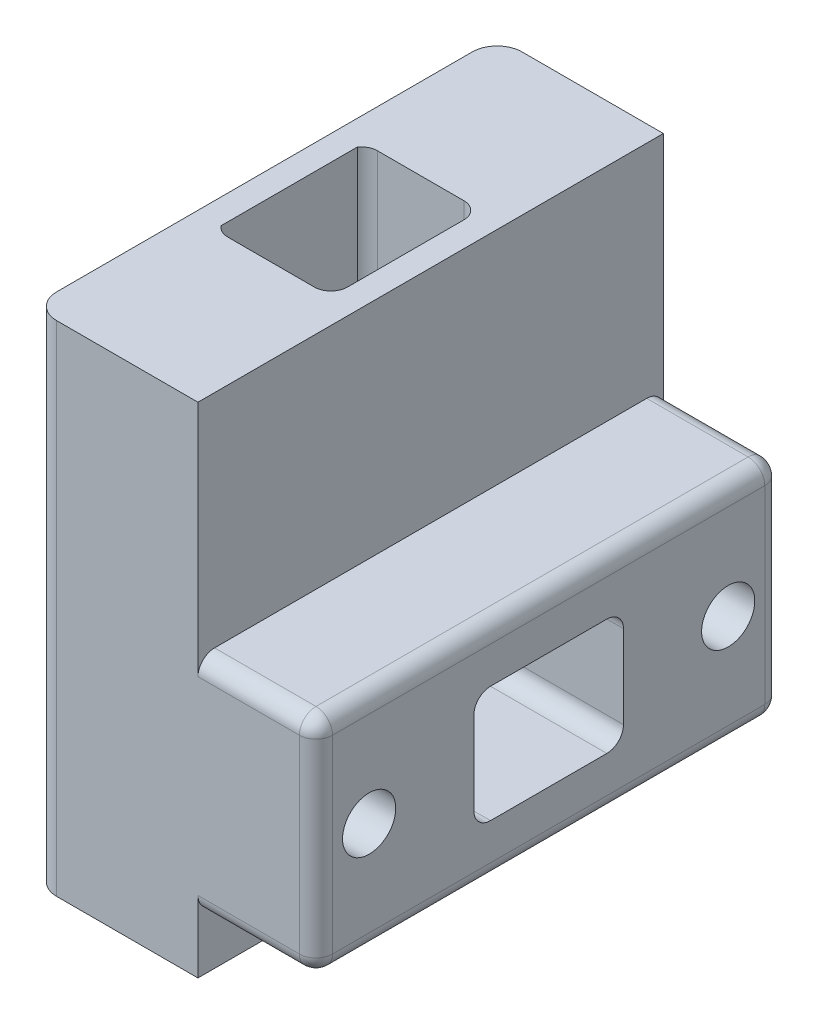
SolidWorks part; units mm, degrees
material "ABS"
ref_plane "前视基准面" through (0, 0, 0) normal (0, 0, 1) x (1, 0, 0)
ref_plane "上视基准面" through (0, 0, 0) normal (0, 1, 0) x (1, 0, 0)
ref_plane "右视基准面" through (0, 0, 0) normal (1, 0, 0) x (0, 0, -1)
sketch "草图1" plane through (0, 0, 0) normal (0, 0, 1) x (1, 0, 0)
  line L0 (0, 30) -> (0, 0)
  line L2 (17.1, 3.3) -> (17.1, 16.7)
  line L3 (17.1, 16.7) -> (10, 16.7)
  line L4 (10, 16.7) -> (10, 30)
  line L5 (10, 30) -> (0, 30)
  line L6 (17.1, 3.3) -> (10, 3.3)
  line L7 (10, 3.3) -> (10, 0)
  line L8 (10, 0) -> (0, 0)
  dimension "D1" = 13.4
  dimension "D2" = 7.1
  dimension "D3" = 13.3
  dimension "D4" = 10
  dimension "D5" = 3.3
extrude "凸台-拉伸1" add sketch "草图1" along normal blind 28 contours L0 L8 L7 L6 L2 L3 L4 L5
sketch "草图2" plane through (17.1, 0, 0) normal (1, 0, 0) x (0, 0, -1)
  line L0 (-28, 10) -> (14.4567, 10) construction
  line L1 (-28, 3.3) -> (-28, 16.7) construction
  line L2 (-14, 16.7) -> (-14, -6.8669) construction
  line L3 (-28, 16.7) -> (0, 16.7) construction
  circle A0 centre (-24.8, 10) radius 1.6
  circle A1 centre (-3.2, 10) radius 1.6
  dimension "D1" = 3.2
  dimension "D2" = 21.6
extrude "切除-拉伸1" cut sketch "草图2" against normal through all and the other way through all
sketch "草图4" plane through (17.1, 0, 0) normal (1, 0, 0) x (0, 0, -1)
  line L0 (0, 10) -> (-37.4348, 10) construction
  line L1 (0, 3.3) -> (0, 16.7) construction
  line L2 (-14, 16.7) -> (-14, -3.8155) construction
  line L3 (-28, 16.7) -> (0, 16.7) construction
  line L5 (-18.5, 13.5) -> (-9.5, 13.5)
  line L6 (-18.5, 13.5) -> (-18.5, 6.5)
  line L7 (-18.5, 6.5) -> (-9.5, 6.5)
  line L8 (-9.5, 13.5) -> (-9.5, 6.5)
  dimension "D1" = 7
  dimension "D2" = 9
extrude "切除-拉伸2" cut sketch "草图4" against normal blind 15.8
sketch "草图5" plane through (0, 30, 0) normal (0, 1, 0) x (1, 0, 0)
  line L0 (5, -28) -> (5, 6.0502) construction
  line L1 (10, -28) -> (0, -28) construction
  line L2 (0, -14) -> (16.5551, -14) construction
  line L3 (0, -28) -> (0, 0) construction
  line L5 (1.5, -18.5) -> (8.5, -18.5)
  line L6 (1.5, -18.5) -> (1.5, -9.5)
  line L7 (1.5, -9.5) -> (8.5, -9.5)
  line L8 (8.5, -18.5) -> (8.5, -9.5)
  dimension "D1" = 9
  dimension "D2" = 7
extrude "切除-拉伸3" cut sketch "草图5" against normal blind 23 contours L8 L7 L6 L5
fillet "圆角1" radius 1.5 2 edges at (0, 15, 28) (0, 15, 0)
fillet "圆角2" radius 1 10 edges at (8.5, 13.5, 14) (8.5, 21.75, 18.5) (8.5, 21.75, 9.5) (12.8, 13.5, 18.5) (12.8, 13.5, 9.5) (9.2, 6.5, 9.5) (9.2, 6.5, 18.5) (1.3, 6.5, 14) (1.3, 10, 18.5) (1.3, 10, 9.5)
fillet "圆角3" radius 1 8 edges at (17.1, 10, 0) (17.1, 3.3, 14) (17.1, 10, 28) (17.1, 16.7, 14) (13.55, 16.7, 28) (13.55, 3.3, 28) (13.55, 3.3, 0) (13.55, 16.7, 0)
